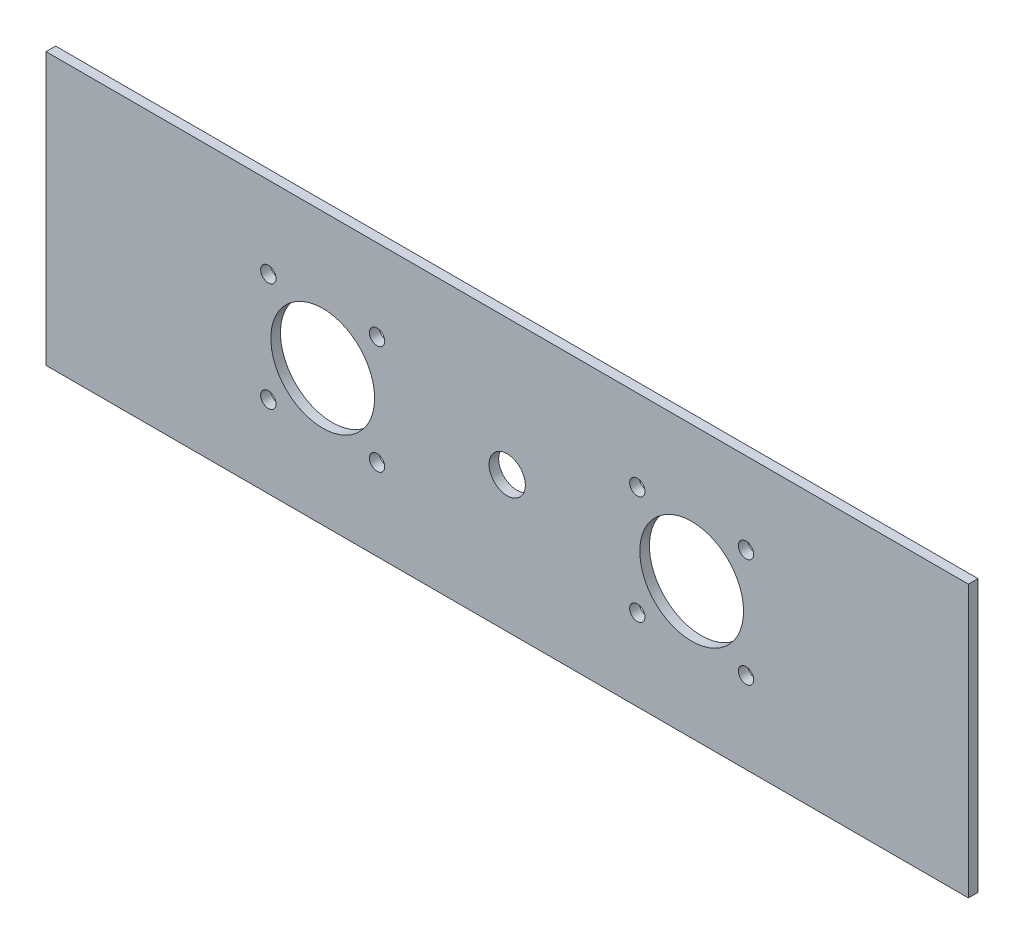
SolidWorks part; units mm, degrees
ref_plane "Front Plane" through (0, 0, 0) normal (0, 0, 1) x (1, 0, 0)
ref_plane "Top Plane" through (0, 0, 0) normal (0, 1, 0) x (1, 0, 0)
ref_plane "Right Plane" through (0, 0, 0) normal (1, 0, 0) x (0, 0, -1)
sketch "Sketch1" plane through (0, 0, 0) normal (0, 0, 1) x (1, 0, 0)
  line L1 (0, 0) -> (304.8, 0)
  line L2 (0, 0) -> (0, 89.8)
  line L3 (0, 89.8) -> (304.8, 89.8)
  line L4 (304.8, 0) -> (304.8, 89.8)
  circle A3 centre (152.4, 44.9) radius 6
  point P5 (114.3, 44.9)
  point P7 (152.4, 44.9)
  point P8 (101.6, 44.9)
  point P9 (203.2, 44.9)
  point P10 (88.9, 44.9)
  point P11 (215.9, 44.9)
  point P13 (88.9, 44.9)
  point P14 (215.9, 44.9)
  circle B0 centre (109.4016, 62.8594) radius 2.54
  circle B1 centre (109.3994, 26.9384) radius 2.54
  circle B2 centre (73.4784, 26.9406) radius 2.54
  circle B3 centre (73.4806, 62.8616) radius 2.54
  circle B4 centre (91.44, 44.9) radius 17.145
  circle B5 centre (195.4006, 62.8616) radius 2.54
  circle B6 centre (231.3216, 62.8594) radius 2.54
  circle B7 centre (231.3194, 26.9384) radius 2.54
  circle B8 centre (195.3984, 26.9406) radius 2.54
  circle B9 centre (213.36, 44.9) radius 17.145
  dimension "D3" = 60.96
  dimension "D4" = 60.96
  dimension "D6" = 12
  dimension "D1" = 89.8
  dimension "D2" = 304.8
sketch_block_instance "Block1-1"
sketch_block "Block1" parameters "D1"=5.08, "D2"=34.29
sketch_block_instance "Block2-1"
sketch_block "Block2" parameters "D1"=5.08, "D2"=34.29
extrude "Boss-Extrude1" add sketch "Sketch1" along normal blind 3.175
